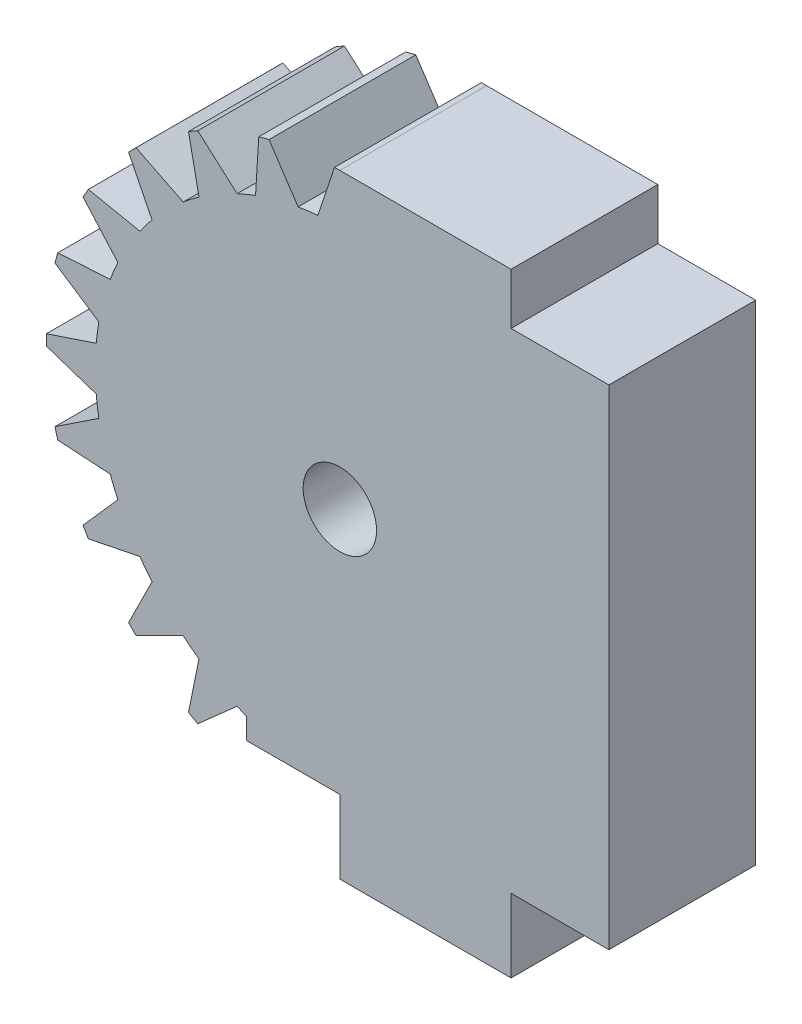
SolidWorks part; units mm, degrees
ref_plane "Front Plane" through (0, 0, 0) normal (0, 0, 1) x (1, 0, 0)
ref_plane "Top Plane" through (0, 0, 0) normal (0, 1, 0) x (1, 0, 0)
ref_plane "Right Plane" through (0, 0, 0) normal (1, 0, 0) x (0, 0, -1)
sketch "Sketch1" plane through (0, 0, 0) normal (0, 0, 1) x (1, 0, 0)
  circle A0 centre (0, 0) radius 10
  dimension "D1" = 20
extrude "Boss-Extrude1" add sketch "Sketch1" along normal blind 6
sketch "Sketch2" plane through (0, 0, 0) normal (0, 0, 1) x (1, 0, 0)
  line L2 (0, 12.65) -> (-0.9, 9.9594)
  line L3 (0, 12.65) -> (0.9, 9.9594)
  arc A0 (0.9, 9.9594) -> (-0.9, 9.9594) centre (0, 0) ccw
  dimension "D1" = 20
  dimension "D3" = 2.8371
  dimension "D4" = 1.8
extrude "Boss-Extrude2" add sketch "Sketch2" along normal blind 6
pattern_circular "CirPattern1" count 24 every 15 about axis through (0, 0, 0) along (0, 0, 1) of "Boss-Extrude2"
sketch "Sketch3" plane through (0, 0, 0) normal (0, 0, 1) x (1, 0, 0)
  circle A0 centre (0, 0) radius 12
  circle A1 centre (0, 0) radius 12.65
  dimension "D1" = 24
  dimension "D2" = 25.3
extrude "Cut-Extrude1" cut sketch "Sketch3" along normal blind 6
sketch "Sketch4" plane through (0, 0, 0) normal (0, 0, 1) x (1, 0, 0)
  line L0 (0, 0) -> (0, 12)
  line L2 (0, 0) -> (-3.8268, -9.2388)
  line L4 (-3.8268, -9.2388) -> (-4.5922, -11.0866)
  arc A0 (-4.5922, -11.0866) -> (0, 12) centre (0, 0) ccw
  arc A1 (0.2181, 11.998) -> (-0.2181, 11.998) centre (0, 0) ccw construction
  arc A2 (-4.2003, -9.0751) -> (-3.447, -9.3871) centre (0, 0) ccw construction
extrude "Cut-Extrude2" cut sketch "Sketch4" along normal blind 6
sketch "Sketch5" plane through (0, 0, 0) normal (0, 0, 1) x (1, 0, 0)
  circle A0 centre (0, 0) radius 1.5
  dimension "D1" = 3
extrude "Cut-Extrude3" cut sketch "Sketch5" along normal blind 6
sketch "Sketch6" plane through (0, 0, 0) normal (0, 0, 1) x (1, 0, 0)
  line L0 (0, 1.5) -> (0, 12)
  line L3 (11, 9.9045) -> (7, 9.9045)
  line L5 (7, 9.9045) -> (7, 12)
  line L6 (11, -10.0955) -> (11, 9.9045)
  line L7 (11, -10.0955) -> (7, -10.0955)
  line L8 (7, -10.0955) -> (7, -13.0955)
  line L10 (0, 12) -> (7, 12)
  line L14 (7, -13.0955) -> (0, -13.0955)
  line L15 (-3.8268, -10.0955) -> (0, -10.0955)
  line L16 (0, -10.0955) -> (0, -13.0955)
  line L17 (-0.574, -1.3858) -> (-3.8268, -9.2388)
  line L18 (-3.8268, -9.2388) -> (-3.8268, -10.0955)
  arc A0 (-0.574, -1.3858) -> (0, 1.5) centre (0, 0) ccw
  dimension "D2" = 2.0955
  dimension "D6" = 7
  dimension "D4" = 20
  dimension "D5" = 4
  dimension "D7" = 3
  dimension "D8" = 7
  dimension "D11" = 4
extrude "Boss-Extrude3" add sketch "Sketch6" along normal blind 6
sketch "Sketch7" [suppressed] plane through (0, 0, 6) normal (0, 0, 1) x (1, 0, 0)
  line L0 (-0.2181, 11.998) -> (7, 12)
  line L1 (7, 12) -> (7, 9.9045)
  line L2 (7, 9.9045) -> (11, 9.9045)
  line L3 (11, 9.9045) -> (11, -10.0955)
  line L4 (11, -10.0955) -> (7, -10.0955)
  line L5 (7, -10.0955) -> (7, -13.0955)
  line L6 (7, -13.0955) -> (0, -13.0955)
  line L7 (0, -13.0955) -> (0, -10.0955)
  line L8 (0, -10.0955) -> (-3.8268, -10.0955)
  line L9 (-3.8268, -10.0955) -> (-3.8268, -9.2388)
  line L10 (-0.2181, 11.998) -> (-0.9, 9.9594)
  line L11 (-1.7084, 9.853) -> (-2.8947, 11.6456)
  line L12 (-2.8947, 11.6456) -> (-3.316, 11.5328)
  line L13 (-3.316, 11.5328) -> (-3.447, 9.3871)
  line L14 (-4.2003, 9.0751) -> (-5.8101, 10.4996)
  line L15 (-5.8101, 10.4996) -> (-6.1879, 10.2815)
  line L16 (-6.1879, 10.2815) -> (-5.7591, 8.1751)
  line L17 (-6.406, 7.6788) -> (-8.3297, 8.6381)
  line L18 (-8.3297, 8.6381) -> (-8.6381, 8.3297)
  line L19 (-8.6381, 8.3297) -> (-7.6788, 6.406)
  line L20 (-8.1751, 5.7591) -> (-10.2815, 6.1879)
  line L21 (-10.2815, 6.1879) -> (-10.4996, 5.8101)
  line L22 (-10.4996, 5.8101) -> (-9.0751, 4.2003)
  line L23 (-9.3871, 3.447) -> (-11.5328, 3.316)
  line L24 (-11.5328, 3.316) -> (-11.6456, 2.8947)
  line L25 (-11.6456, 2.8947) -> (-9.853, 1.7084)
  line L26 (-9.9594, 0.9) -> (-11.998, 0.2181)
  line L27 (-11.998, 0.2181) -> (-11.998, -0.2181)
  line L28 (-11.998, -0.2181) -> (-9.9594, -0.9)
  line L29 (-9.853, -1.7084) -> (-11.6456, -2.8947)
  line L30 (-11.6456, -2.8947) -> (-11.5328, -3.316)
  line L31 (-11.5328, -3.316) -> (-9.3871, -3.447)
  line L32 (-9.0751, -4.2003) -> (-10.4996, -5.8101)
  line L33 (-10.4996, -5.8101) -> (-10.2815, -6.1879)
  line L34 (-10.2815, -6.1879) -> (-8.1751, -5.7591)
  line L35 (-7.6788, -6.406) -> (-8.6381, -8.3297)
  line L36 (-7.6788, -6.406) -> (-8.6381, -8.3297) construction
  line L37 (-8.6381, -8.3297) -> (-8.3297, -8.6381)
  line L38 (-8.3297, -8.6381) -> (-6.406, -7.6788)
  line L39 (-5.7591, -8.1751) -> (-6.1879, -10.2815)
  line L40 (-6.1879, -10.2815) -> (-5.8101, -10.4996)
  line L41 (-5.8101, -10.4996) -> (-4.2003, -9.0751)
  circle A0 centre (0, 0) radius 1.5
  arc A1 (-0.9, 9.9594) -> (-1.7084, 9.853) centre (0, 0) ccw
  arc A2 (-3.447, 9.3871) -> (-4.2003, 9.0751) centre (0, 0) ccw
  arc A3 (-5.7591, 8.1751) -> (-6.406, 7.6788) centre (0, 0) ccw
  arc A4 (-7.6788, 6.406) -> (-8.1751, 5.7591) centre (0, 0) ccw
  arc A5 (-9.0751, 4.2003) -> (-9.3871, 3.447) centre (0, 0) ccw
  arc A6 (-9.853, 1.7084) -> (-9.9594, 0.9) centre (0, 0) ccw
  arc A7 (-4.2003, -9.0751) -> (-3.8268, -9.2388) centre (0, 0) ccw
  arc A8 (-6.406, -7.6788) -> (-5.7591, -8.1751) centre (0, 0) ccw
  arc A9 (-8.1751, -5.7591) -> (-7.6788, -6.406) centre (0, 0) ccw
  arc A10 (-9.3871, -3.447) -> (-9.0751, -4.2003) centre (0, 0) ccw
  arc A11 (-9.9594, -0.9) -> (-9.853, -1.7084) centre (0, 0) ccw
